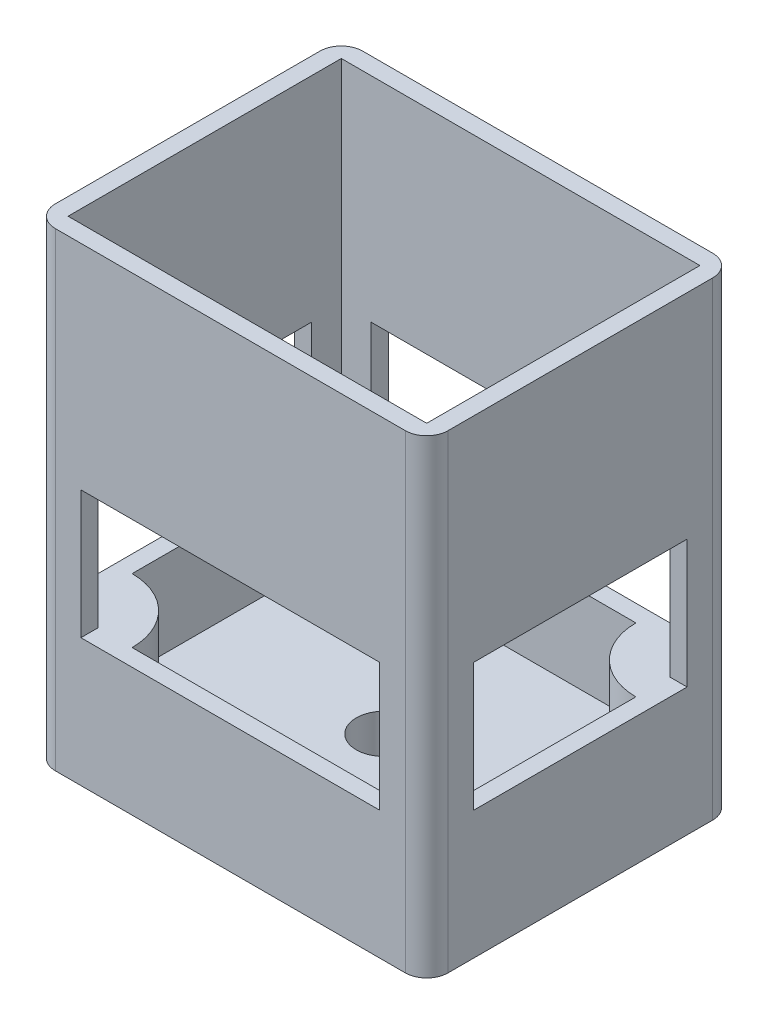
SolidWorks part; units mm, degrees
ref_plane "Front Plane" through (0, 0, 0) normal (0, 0, 1) x (1, 0, 0)
ref_plane "Top Plane" through (0, 0, 0) normal (0, 1, 0) x (1, 0, 0)
ref_plane "Right Plane" through (0, 0, 0) normal (1, 0, 0) x (0, 0, -1)
sketch "Sketch1" plane through (0, 0, 0) normal (0, 1, 0) x (1, 0, 0)
  line L1 (-23, 18) -> (23, 18)
  line L2 (-23, 18) -> (-23, -18)
  line L3 (-23, -18) -> (23, -18)
  line L4 (23, 18) -> (23, -18)
  line L5 (-21, 16) -> (21, 16)
  line L6 (-21, 16) -> (-21, -16)
  line L7 (-21, -16) -> (21, -16)
  line L8 (21, 16) -> (21, -16)
  point P8 (0, -16)
  point P9 (-21, 0)
  dimension "D1" = 42
  dimension "D2" = 32
  dimension "D3" = 2
  dimension "D4" = 2
  dimension "D5" = 2
  dimension "D6" = 2
extrude "Boss-Extrude1" add sketch "Sketch1" along normal blind 55
sketch "Sketch2" plane through (0, 0, 0) normal (0, -1, 0) x (1, 0, 0)
  line L4 (-21, 16) -> (-21, -16)
  line L5 (21, 16) -> (-21, 16)
  line L6 (21, -16) -> (21, 16)
  line L7 (-21, -16) -> (21, -16)
  line L8 (-21, 16) -> (-21, -16)
  line L9 (21, 16) -> (-21, 16)
  line L10 (21, -16) -> (21, 16)
  line L11 (-21, -16) -> (21, -16)
  dimension "D1" = 0
extrude "Boss-Extrude2" add sketch "Sketch2" against normal blind 5
fillet "Fillet1" radius 2.5 4 edges at (-23, 27.5, -18) (23, 27.5, -18) (23, 27.5, 18) (-23, 27.5, 18)
sketch "Sketch4" plane through (0, 5, 0) normal (0, 1, 0) x (1, 0, 0)
  line L0 (21, -16) -> (-21, -16) construction
  line L1 (-21, 16) -> (-21, -16) construction
  line L2 (-21, 16) -> (21, 16) construction
  line L3 (21, 16) -> (21, -16) construction
  line L8 (-21, -16) -> (21, -16)
  line L9 (-21, 16) -> (-21, -16)
  line L10 (21, 16) -> (-21, 16)
  line L11 (21, -16) -> (21, 16)
  line L12 (-21, -16) -> (-13.5, -16)
  line L13 (-21, -8.5) -> (-21, -16)
  line L14 (21, 16) -> (13.5, 16)
  line L15 (21, 8.5) -> (21, 16)
  arc A0 (-13.5, -16) -> (-21, -8.5) centre (-21, -16) ccw
  arc A1 (13.5, 16) -> (21, 8.5) centre (21, 16) ccw
  dimension "D1" = 7.5
  dimension "D2" = 7.5
  dimension "D3" = 0
extrude "Boss-Extrude3" add sketch "Sketch4" along normal blind 10
sketch "Sketch3" plane through (23, 0, -5) normal (-1, 0, 0) x (0, 0, 1)
  line L1 (-7.5, 30) -> (17.5, 30)
  line L2 (-7.5, 30) -> (-7.5, 15)
  line L3 (-7.5, 15) -> (17.5, 15)
  line L4 (17.5, 30) -> (17.5, 15)
  line L7 (-3.5, 15) -> (-11, 15) construction
  point P7 (5, 15)
  dimension "D2" = 25
  dimension "D3" = 15
extrude "Cut-Extrude1" cut sketch "Sketch3" along normal through all
sketch "Sketch5" plane through (0, 0, 18) normal (0, 0, 1) x (1, 0, 0)
  line L0 (-13.5, 15) -> (-21, 15) construction
  line L1 (-17.5, 30) -> (17.5, 30)
  line L2 (-17.5, 30) -> (-17.5, 15)
  line L3 (-17.5, 15) -> (17.5, 15)
  line L4 (17.5, 30) -> (17.5, 15)
  point P4 (0, 15)
  dimension "D1" = 35
  dimension "D2" = 15
extrude "Cut-Extrude2" cut sketch "Sketch5" against normal through all
sketch "Sketch7" plane through (0, 5, 0) normal (0, 1, 0) x (1, 0, 0)
  circle A0 centre (0, 0) radius 3.25
  dimension "D1" = 6.5
extrude "Cut-Extrude3" cut sketch "Sketch7" against normal up to next contours A0
